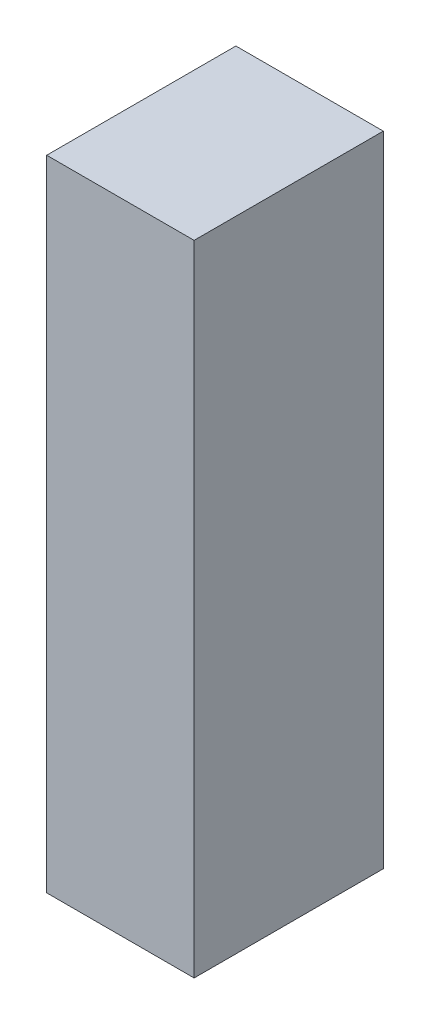
SolidWorks part; units mm, degrees
ref_plane "Alzado" through (0, 0, 0) normal (0, 0, 1) x (1, 0, 0)
ref_plane "Planta" through (0, 0, 0) normal (0, 1, 0) x (1, 0, 0)
ref_plane "Vista lateral" through (0, 0, 0) normal (1, 0, 0) x (0, 0, -1)
sketch "Croquis1" plane through (0, 0, 0) normal (0, 1, 0) x (1, 0, 0)
  line L1 (150, 192.5) -> (-150, 192.5)
  line L2 (150, 192.5) -> (150, -192.5)
  line L3 (150, -192.5) -> (-150, -192.5)
  line L4 (-150, 192.5) -> (-150, -192.5)
  line L5 (150, 192.5) -> (-150, -192.5) construction
  line L6 (150, -192.5) -> (-150, 192.5) construction
  point P0 (0, 0)
  dimension "D1" = 300
  dimension "D2" = 385
extrude "Saliente-Extruir1" add sketch "Croquis1" along normal blind 1300
